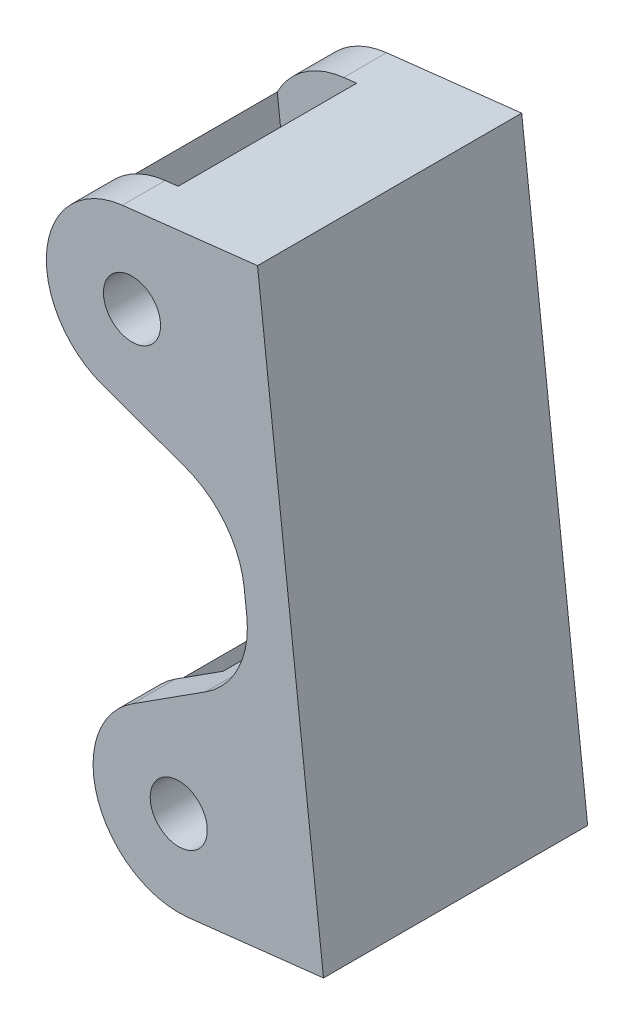
SolidWorks part; units mm, degrees
ref_plane "Front Plane" through (0, 0, 0) normal (0, 0, 1) x (1, 0, 0)
ref_plane "Top Plane" through (0, 0, 0) normal (0, 1, 0) x (1, 0, 0)
ref_plane "Right Plane" through (0, 0, 0) normal (1, 0, 0) x (0, 0, -1)
sketch "Sketch2" plane through (137.5485, -674.1529, 0) normal (0, 0, -1) x (0.9937, 0.1122, 0)
  line L0 (-92.7733, -210.4838) -> (9.525, -316.7444) construction
  line L1 (9.526, -375.0556) -> (-92.7687, -481.3197) construction
  line L2 (9.525, -304.7444) -> (28.575, -304.7444)
  line L3 (28.575, -304.7444) -> (28.575, -387.0556)
  line L4 (28.575, -387.0556) -> (9.526, -387.0556)
  line L5 (4.2237, -327.5099) -> (15.1355, -332.8831)
  line L6 (4.2237, -364.2906) -> (15.1365, -358.9156)
  line L7 (28.575, -345.9) -> (4.5557, -345.9) construction
  line L8 (22.225, -347.5226) -> (22.225, -344.2767)
  line L9 (4.2237, -327.5099) -> (4.2237, -364.2906) construction
  circle A0 centre (9.526, -375.0556) radius 4
  circle A1 centre (9.525, -316.7444) radius 4
  arc A2 (9.525, -304.7444) -> (4.2237, -327.5099) centre (9.525, -316.7444) ccw
  arc A3 (4.2237, -364.2906) -> (9.526, -387.0556) centre (9.526, -375.0556) ccw
  arc A4 (15.1365, -358.9156) -> (22.225, -347.5226) centre (9.525, -347.5226) ccw
  arc A5 (15.1355, -332.8831) -> (22.225, -344.2767) centre (9.525, -344.2767) cw
  point P23 (22.225, -355.4242)
  point P26 (22.225, -336.3742)
  dimension "D1" = 8
  dimension "D2" = 24
  dimension "D6" = 12.7
  dimension "D3" = 19.05
  dimension "D4" = 6.35
  dimension "D5" = 19.05
extrude "Boss-Extrude1" add sketch "Sketch2" along normal mid plane 37
sketch "Sketch3" plane through (140.1346, -673.0535, 0) normal (0, 0, -1) x (0.9937, 0.1122, 0)
  line L1 (-3.1344, -296.3798) -> (8.6553, -296.3798)
  line L2 (-3.1344, -296.3798) -> (-3.1344, -392.3849)
  line L3 (-3.1344, -392.3849) -> (8.6553, -392.3849)
  line L4 (8.6553, -296.3798) -> (8.6553, -392.3849)
  dimension "D1" = 12
extrude "Cut-Extrude1" cut sketch "Sketch3" against normal mid plane 25
sketch3d "3DSketch1"
  line L0 (111.4603, -358.341, -18.5) -> (111.4603, -358.341, 18.5) construction
  line L1 (111.4603, -358.341, -18.5) -> (111.4603, -358.341, 18.5) construction
  line L2 (111.4603, -358.341, -18.5) -> (111.4603, -358.341, 18.5) construction
  line L3 (104.9162, -300.3981, 18.5) -> (104.9162, -300.3981, -18.5) construction
  line L6 (104.9162, -300.3981, -18.5) -> (104.9162, -300.3981, 18.5) construction
  line L7 (104.9162, -300.3981, -18.5) -> (104.9162, -300.3981, 18.5) construction
ref_plane "Plane1" through (70.0946, 7.9166, 0) normal (-0.9937, -0.1122, 0) x (-0.0035, 0.0313, 0.9995)
